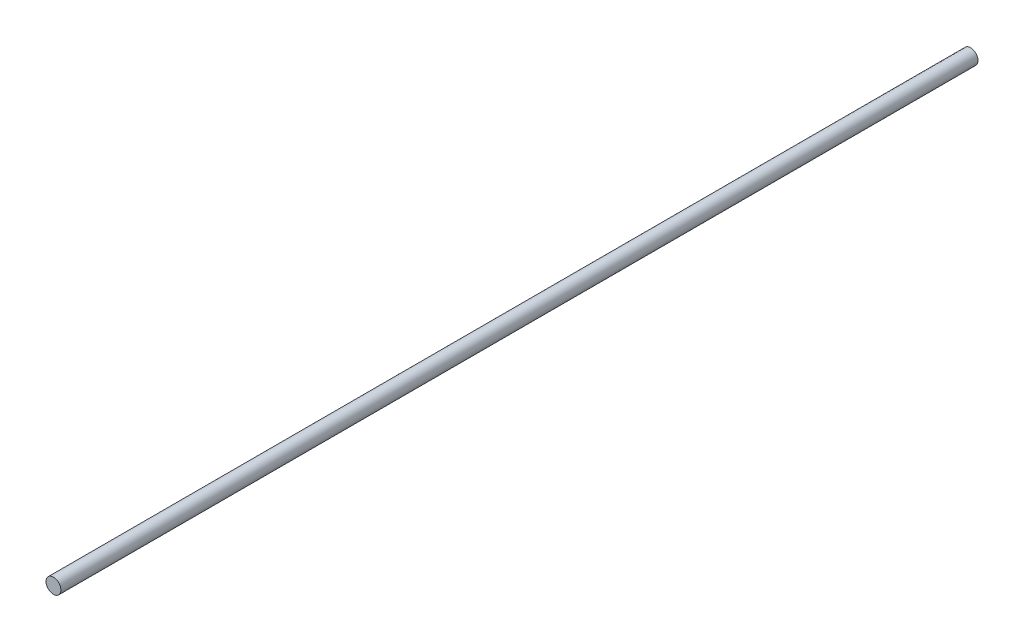
SolidWorks part; units mm, degrees
ref_plane "Plano frontal" through (0, 0, 0) normal (0, 0, 1) x (1, 0, 0)
ref_plane "Plano superior" through (0, 0, 0) normal (0, 1, 0) x (1, 0, 0)
ref_plane "Plano direito" through (0, 0, 0) normal (1, 0, 0) x (0, 0, -1)
ref_plane "Plano1" through (0, 0, 0) normal (0, -1, 0) x (1, 0, 0)
sketch "Esboço1" plane through (0, 0, 0) normal (0, -1, 0) x (1, 0, 0)
  line L0 (4.0802, 502.48) -> (0, 502.48)
  line L1 (0, 502.48) -> (0, 0)
  line L2 (0, 0) -> (4.0802, 0)
  line L3 (4.0802, 0) -> (4.0802, 502.48)
  line L4 (0, 502.48) -> (0, 0) construction
  dimension "D1" = 502.48
revolve "Revolução1" add sketch "Esboço1" angle 360 about L4
